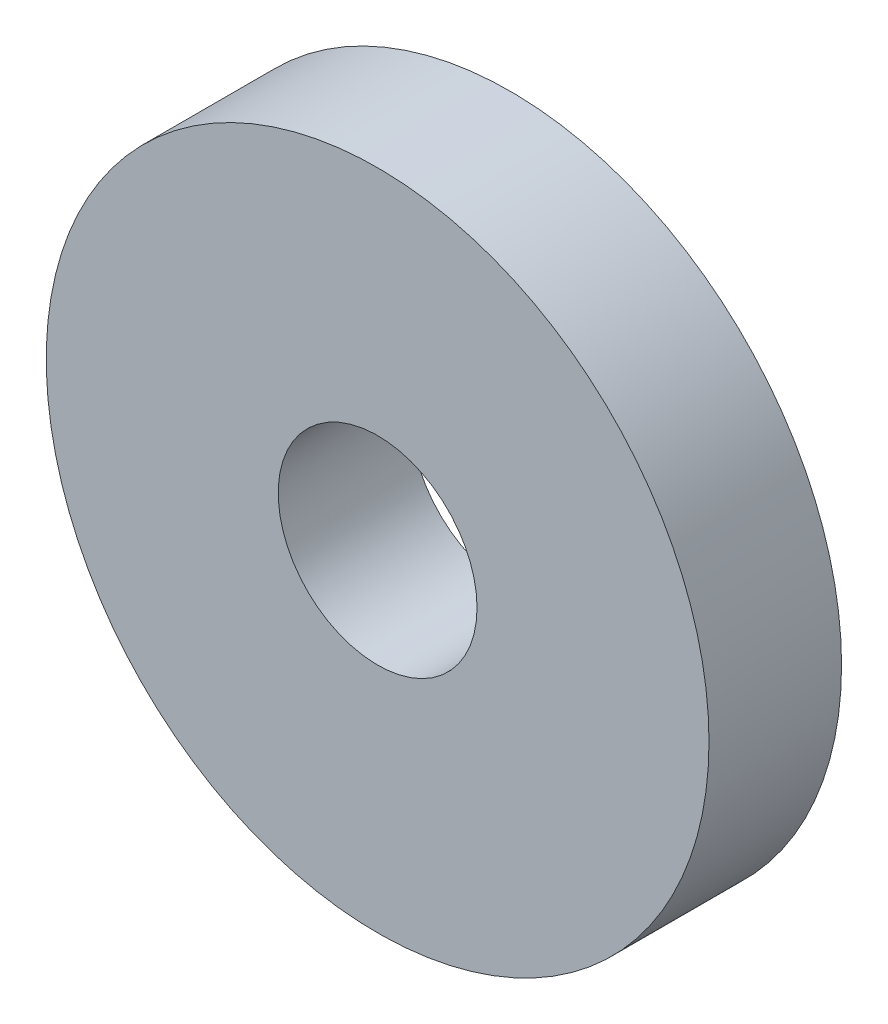
SolidWorks part; units mm, degrees
ref_plane "前视基准面" through (0, 0, 0) normal (0, 0, 1) x (1, 0, 0)
ref_plane "上视基准面" through (0, 0, 0) normal (0, 1, 0) x (1, 0, 0)
ref_plane "右视基准面" through (0, 0, 0) normal (1, 0, 0) x (0, 0, -1)
sketch "草图1" plane through (0, 0, 0) normal (1, 0, 0) x (0, 0, -1)
  line L0 (0, 0) -> (20.7993, 0) construction
  line L1 (0, 3) -> (0, 10)
  line L2 (0, 10) -> (4, 10)
  line L3 (4, 10) -> (4, 3)
  line L5 (0, 3) -> (4, 3)
  dimension "D1" = 6
  dimension "D2" = 20
  dimension "D3" = 4
revolve "旋转1" add sketch "草图1" angle 360 about L0
